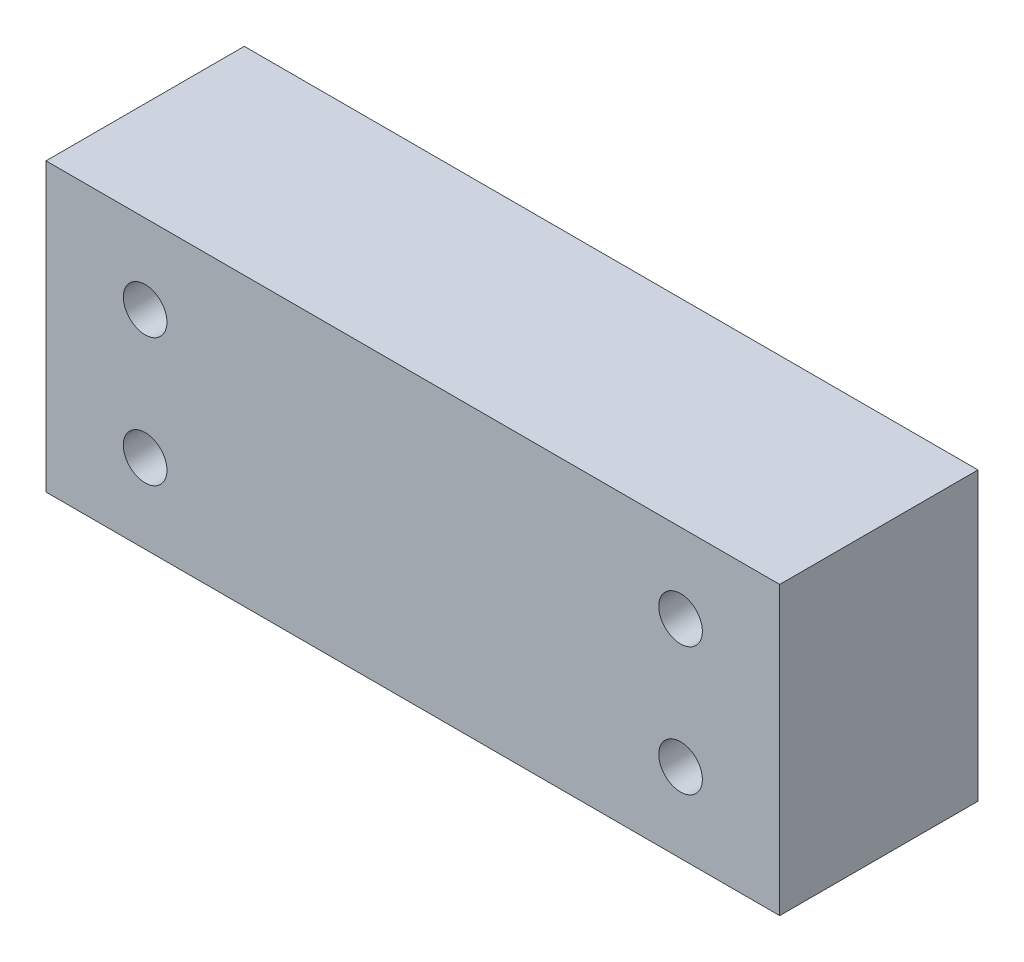
SolidWorks part; units mm, degrees
material "PETG"
ref_plane "Front Plane" through (0, 0, 0) normal (0, 0, 1) x (1, 0, 0)
ref_plane "Top Plane" through (0, 0, 0) normal (0, 1, 0) x (1, 0, 0)
ref_plane "Right Plane" through (0, 0, 0) normal (1, 0, 0) x (0, 0, -1)
sketch "Sketch1" plane through (0, 0, 0) normal (0, 0, 1) x (1, 0, 0)
  line L0 (0, 10.85) -> (0, -10.85) construction
  line L1 (-27.75, -10.85) -> (27.75, -10.85)
  line L2 (-27.75, -10.85) -> (-27.75, 10.85)
  line L3 (-27.75, 10.85) -> (27.75, 10.85)
  line L4 (27.75, -10.85) -> (27.75, 10.85)
  line L5 (-27.75, -10.85) -> (27.75, 10.85) construction
  line L6 (-27.75, 10.85) -> (27.75, -10.85) construction
  line L7 (-27.75, 0) -> (27.75, 0) construction
  circle A0 centre (20.25, 4.85) radius 1.65
  circle A1 centre (-20.25, 4.85) radius 1.65
  circle A2 centre (20.25, -4.85) radius 1.65
  circle A3 centre (-20.25, -4.85) radius 1.65
  point P0 (0, 0)
  dimension "D3" = 3.3
  dimension "D4" = 7.5
  dimension "D1" = 55.5
  dimension "D2" = 21.7
  dimension "D5" = 6
extrude "Boss-Extrude1" add sketch "Sketch1" along normal blind 15
